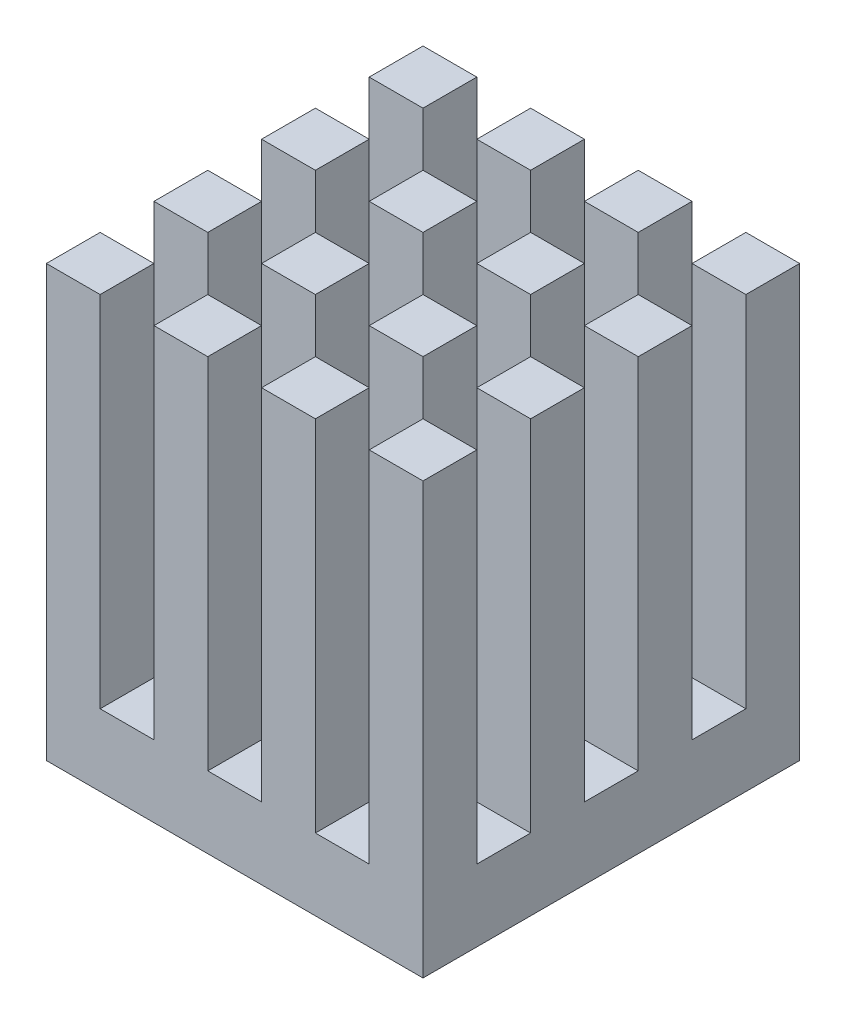
SolidWorks part; units mm, degrees
material "Copper"
ref_plane "Front Plane" through (0, 0, 0) normal (0, 0, 1) x (1, 0, 0)
ref_plane "Top Plane" through (0, 0, 0) normal (0, 1, 0) x (1, 0, 0)
ref_plane "Right Plane" through (0, 0, 0) normal (1, 0, 0) x (0, 0, -1)
sketch "Sketch1" plane through (0, 0, 0) normal (0, 1, 0) x (1, 0, 0)
  line L1 (-5.25, 5.25) -> (5.25, 5.25)
  line L2 (-5.25, 5.25) -> (-5.25, -5.25)
  line L3 (-5.25, -5.25) -> (5.25, -5.25)
  line L4 (5.25, 5.25) -> (5.25, -5.25)
  line L5 (-5.25, 5.25) -> (5.25, -5.25) construction
  line L6 (-5.25, -5.25) -> (5.25, 5.25) construction
  point P0 (0, 0)
  dimension "D1" = 10.5
extrude "Boss-Extrude1" add sketch "Sketch1" along normal blind 2
sketch "Sketch2" plane through (0, 2, 0) normal (0, 1, 0) x (1, 0, 0)
  line L1 (-5.25, 5.25) -> (-3.75, 5.25)
  line L2 (-5.25, 5.25) -> (-5.25, 3.75)
  line L3 (-5.25, 3.75) -> (-3.75, 3.75)
  line L4 (-3.75, 5.25) -> (-3.75, 3.75)
  dimension "D1" = 1.5
  dimension "D2" = 1.5
extrude "Boss-Extrude2" add sketch "Sketch2" along normal blind 10
pattern_linear "LPattern1" count 4 spacing 3 along (1, 0, 0) count 4 spacing 3 along (0, 0, 1) of "Boss-Extrude2"
